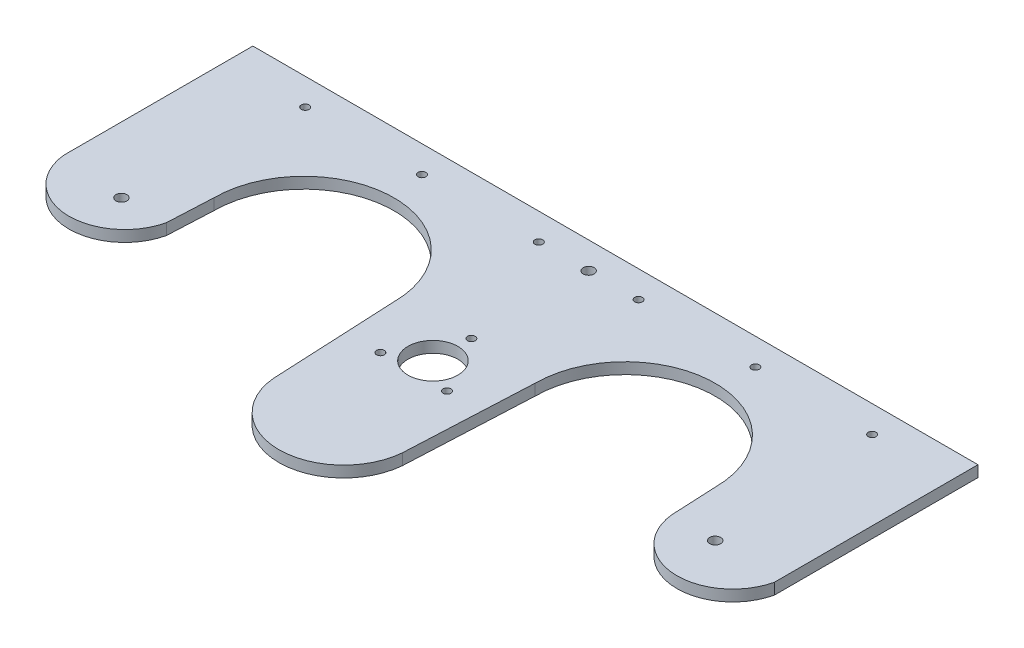
SolidWorks part; units mm, degrees
ref_plane "Plan de face" through (0, 0, 0) normal (0, 0, 1) x (1, 0, 0)
ref_plane "Plan de dessus" through (0, 0, 0) normal (0, 1, 0) x (1, 0, 0)
ref_plane "Plan de droite" through (0, 0, 0) normal (1, 0, 0) x (0, 0, -1)
sketch "Esquisse2" plane through (0, 0, 0) normal (0, 1, 0) x (1, 0, 0)
  line L1 (0, 0) -> (298, 0)
  line L2 (0, 0) -> (0, 145)
  line L3 (0, 145) -> (298, 145)
  line L4 (298, 0) -> (298, 145)
  dimension "D1" = 145
  dimension "D2" = 298
extrude "Boss.-Extru.1" add sketch "Esquisse2" along normal blind 4.6
sketch "Esquisse3" plane through (0, 4.6, 0) normal (0, 1, 0) x (1, 0, 0)
  line L0 (0, 145) -> (0, 120) construction
  line L1 (0, 145) -> (0, 0) construction
  line L2 (0, 120) -> (298, 120) construction
  line L3 (298, 0) -> (298, 145) construction
  line L4 (149, 145) -> (149, 0) construction
  line L5 (0, 0) -> (298, 0) construction
  line L6 (75, 120) -> (75, 0) construction
  line L7 (225, 120) -> (225, 0) construction
  line L8 (0, 83) -> (298, 83) construction
  line L9 (46, 83) -> (42, 0)
  line L14 (120, 83) -> (124, 0)
  line L15 (124, 0) -> (42, 0)
  line L20 (298, 145) -> (0, 145) construction
  line L21 (174, 0) -> (256, 0)
  line L22 (252, 83) -> (256, 0)
  line L23 (178, 83) -> (174, 0)
  arc A2 (46, 83) -> (120, 83) centre (83, 83) cw
  arc A4 (252, 83) -> (178, 83) centre (215, 83) ccw
  point P24 (42, 0)
  point P29 (124, 0)
  dimension "D4" = 37
  dimension "D1" = 25
  dimension "D2" = 66
  dimension "D3" = 82
  dimension "D5" = 25
extrude "creux_stockage_verre" cut sketch "Esquisse3" against normal blind 46.6
sketch "Esquisse6" plane through (0, 4.6, 0) normal (0, 1, 0) x (1, 0, 0)
  line L0 (149, 145) -> (149, 0) construction
  line L1 (298, 145) -> (0, 145) construction
  line L2 (124, 0) -> (174, 0) construction
  circle A0 centre (149, 70) radius 10.25
  point P1 (149, 70)
  dimension "D2" = 20.5
  dimension "D1" = 70
extrude "trou_bille" cut sketch "Esquisse6" against normal through all
sketch "Esquisse7" plane through (0, 4.6, 0) normal (0, 1, 0) x (1, 0, 0)
  line L0 (0, 145) -> (0, 0) construction
  line L1 (298, 145) -> (0, 145) construction
  line L2 (149, 145) -> (149, 0) construction
  line L3 (124, 0) -> (174, 0) construction
  circle A0 centre (32.5, 134) radius 1.6
  circle A1 centre (80.5, 134) radius 1.6
  circle A2 centre (128.5, 134) radius 1.6
  circle A3 centre (217.5, 134) radius 1.6
  circle A4 centre (169.5, 134) radius 1.6
  circle A5 centre (265.5, 134) radius 1.6
  point P0 (32.5, 134)
  dimension "D3" = 3.2
  dimension "D1" = 32.5
  dimension "D2" = 11
  dimension "D4" = 3
extrude "Enlèv. mat.-Extru.3" cut sketch "Esquisse7" against normal through all
sketch "Esquisse9" plane through (0, 4.6, 0) normal (0, 1, 0) x (1, 0, 0)
  line L0 (124, 0) -> (120, 83) construction
  line L1 (178, 83) -> (174, 0) construction
  line L2 (123.1011, 18.6515) -> (120.0586, -9.9421)
  line L3 (120.0586, -9.9421) -> (178.7898, -9.9421)
  line L4 (178.7898, -9.9421) -> (174.8989, 18.6515)
  arc A0 (123.1011, 18.6515) -> (174.8989, 18.6515) centre (149, 70) ccw
extrude "Enlèv. mat.-Extru.7" cut sketch "Esquisse9" against normal blind 29
sketch "Esquisse12" plane through (0, 4.6, 0) normal (0, 1, 0) x (1, 0, 0)
  line L0 (0, 0) -> (42, 0) construction
  line L1 (17, 0) -> (37, 0) construction
  line L2 (17, 0) -> (17, 54) construction
  line L3 (17, 54) -> (37, 54) construction
  line L4 (37, 0) -> (37, 54) construction
  line L5 (0, 145) -> (0, 0) construction
  line L6 (17, 54) -> (37, 54) construction
  line L7 (17, 54) -> (17, 74) construction
  line L8 (17, 74) -> (37, 74) construction
  line L9 (37, 54) -> (37, 74) construction
  line L10 (149, 70) -> (149, 171.4441) construction
  line L11 (149, 171.4441) -> (149, -44.8206) construction
  line L12 (80.5, 134) -> (184.9359, 134) construction
  line L13 (27, 64) -> (271, 64) construction
  circle A0 centre (27, 64) radius 2.25
  circle A1 centre (149, 134) radius 2.25
  circle A2 centre (271, 64) radius 2.25
  point P21 (149, 63.3118)
  dimension "D6" = 10
  dimension "D7" = 4.5
  dimension "D10" = 4.5
  dimension "D11" = 4.5
  dimension "D1" = 54
  dimension "D2" = 20
  dimension "D3" = 20
  dimension "D4" = 17
  dimension "D5" = 10
  dimension "D8" = 122
  dimension "D9" = 122
sketch "Esquisse14" plane through (0, 4.6, 0) normal (0, 1, 0) x (1, 0, 0)
  line L0 (46, 83) -> (42, 0) construction
  line L1 (0, 145) -> (0, 0) construction
  line L2 (0, 71.7078) -> (298, 71.7078) construction
  line L3 (298, 0) -> (298, 145) construction
  line L4 (45.1014, 64.3544) -> (252.8986, 64.3544) construction
  line L5 (256, 0) -> (252, 83) construction
  line L6 (0, 71.7078) -> (-22.1588, -9.529)
  line L7 (-22.1588, -9.529) -> (50.381, -9.529)
  line L8 (50.381, -9.529) -> (45.1014, 64.3544)
  line L12 (252.8986, 64.3544) -> (243.7072, -12.3737)
  line L13 (243.7072, -12.3737) -> (332.1502, -12.3737)
  line L14 (332.1502, -12.3737) -> (298, 71.7078)
  line L15 (80.5086, 31) -> (206.1294, 31) construction
  line L16 (298, 145) -> (0, 145) construction
  arc A0 (45.1014, 64.3544) -> (0, 71.7078) centre (22.7978, 69.5466) cw
  arc A3 (298, 71.7078) -> (252.8986, 64.3544) centre (275.6964, 66.5157) cw
  dimension "D1" = 22.9
  dimension "D2" = 22.9
  dimension "D3" = 114
sketch "Esquisse15" plane through (0, 4.6, 0) normal (0, 1, 0) x (1, 0, 0)
  line L0 (178, 83) -> (174.8989, 18.6515) construction
  line L1 (123.1011, 18.6515) -> (120, 83) construction
  line L3 (298, 145) -> (0, 145) construction
  arc A0 (175.494, 31) -> (122.506, 31) centre (149, 32.5386) cw
  arc A1 (175.494, 31) -> (122.506, 31) centre (149, 95.7936) cw
  point P11 (149, 6)
  point P18 (122.506, 31)
  dimension "D1" = 139
sketch "Esquisse17" plane through (0, 4.6, 0) normal (0, 1, 0) x (1, 0, 0)
  line L1 (149, 85.81) -> (135.3081, 62.095) construction
  line L2 (135.3081, 62.095) -> (162.6919, 62.095) construction
  line L3 (162.6919, 62.095) -> (149, 85.81) construction
  circle A0 centre (149, 70) radius 7.905 construction
  circle A1 centre (149, 85.81) radius 1.6
  circle A2 centre (135.3081, 62.095) radius 1.6
  circle A3 centre (162.6919, 62.095) radius 1.6
  dimension "D2" = 3.2
  dimension "D3" = 3.2
  dimension "D4" = 3.2
  dimension "D1" = 15.81
extrude "Enlèv. mat.-Extru.14" cut sketch "Esquisse17" against normal blind 4.6
extrude "Boss.-Extru.5" add sketch "Esquisse15" against normal blind 4.6
sketch "Esquisse18" plane through (0, 4.6, 0) normal (0, 1, 0) x (1, 0, 0)
  line L0 (80.5086, 31) -> (206.1294, 31) construction
  line L1 (123.1011, 18.6515) -> (120, 83) construction
  line L2 (178, 83) -> (174.8989, 18.6515) construction
  line L3 (175.494, 31) -> (178.8476, -7.0098)
  line L4 (178.8476, -7.0098) -> (115.9732, -7.0098)
  line L5 (115.9732, -7.0098) -> (122.506, 31)
  arc A0 (122.506, 31) -> (175.494, 31) centre (149, 33.2867) ccw
extrude "Enlèv. mat.-Extru.15" cut sketch "Esquisse18" against normal blind 4.6
extrude "Enlèv. mat.-Extru.16" cut sketch "Esquisse14" against normal blind 4.6
extrude "Enlèv. mat.-Extru.17" cut sketch "Esquisse12" against normal blind 10
